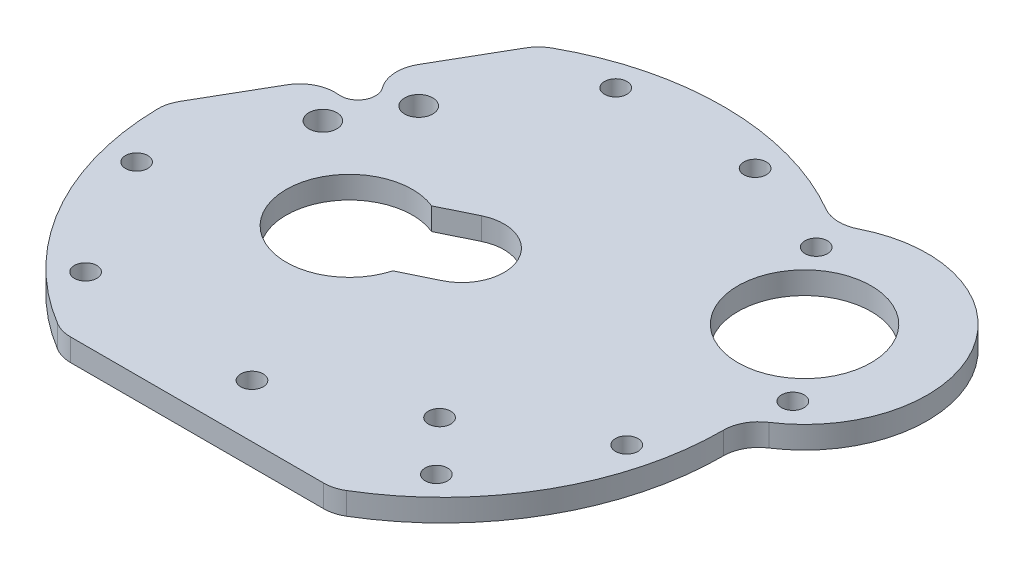
SolidWorks part; units mm, degrees
ref_plane "Front Plane" through (0, 0, 0) normal (0, 0, 1) x (1, 0, 0)
ref_plane "Top Plane" through (0, 0, 0) normal (0, 1, 0) x (1, 0, 0)
ref_plane "Right Plane" through (0, 0, 0) normal (1, 0, 0) x (0, 0, -1)
sketch "Sketch2" plane through (0, 0, 0) normal (0, 1, 0) x (1, 0, 0)
  line L0 (-20.6284, 34.2705) -> (-39.9933, 0.7295)
  line L1 (-19.3649, -35) -> (19.3649, -35)
  line L2 (0, 0) -> (-9.9332, 34.6025) construction
  line L3 (0, 0) -> (-34.9332, -8.6988) construction
  line L4 (0, 0) -> (32.7032, 18.8812) construction
  line L5 (0, 40) -> (0, 0) construction
  line L6 (0.2426, -27.4303) -> (18.2185, -18.6629) construction
  line L7 (0, 0) -> (10.8543, -22.2546) construction
  line L8 (-1.1037, 3.8447) -> (-11.8892, -1.4157) construction
  line L9 (24.0255, 29.2228) -> (41.3808, 8.5396) construction
  line L10 (32.7032, 18.8812) -> (32.7032, 36.3812) construction
  line L11 (-9.9332, 34.6025) -> (-34.9332, -8.6988) construction
  line L12 (0, 0) -> (-22.4332, 12.9518) construction
  line L13 (-25, -25.9037) -> (25, -25.9037) construction
  line L14 (0, 0) -> (0, -25.9037) construction
  line L15 (-3.7339, 9.2375) -> (-8.4902, 6.9177)
  line L16 (1.5265, -1.548) -> (-3.2297, -3.8678)
  arc A0 (-39.9933, 0.7295) -> (-19.3649, -35) centre (0, 0) ccw
  circle A1 centre (0.2426, -27.4303) radius 1.6 construction
  arc A2 (39.8928, 2.9263) -> (22.4806, 33.0851) centre (32.7032, 18.8812) ccw
  circle A3 centre (32.7032, 18.8812) radius 9.5
  circle A4 centre (-9.9332, 34.6025) radius 1.6
  circle A5 centre (34.9332, -8.6988) radius 1.6
  circle A6 centre (24.0255, 29.2228) radius 1.6
  circle A7 centre (41.3808, 8.5396) radius 1.6
  circle A8 centre (9.9332, 34.6025) radius 1.6
  circle A9 centre (18.2185, -18.6629) radius 1.6
  circle A10 centre (-25, -25.9037) radius 1.6
  circle A11 centre (0.2426, -27.4303) radius 1.6
  circle A12 centre (25, -25.9037) radius 1.6
  circle A13 centre (-34.9332, -8.6988) radius 1.6
  arc A15 (-8.4902, 6.9177) -> (-3.2297, -3.8678) centre (-11.8892, -1.4157) ccw
  arc A16 (1.5265, -1.548) -> (-3.7339, 9.2375) centre (-1.1037, 3.8447) ccw
  arc A17 (19.3649, -35) -> (39.8928, 2.9263) centre (0, 0) ccw
  circle A18 centre (0, 0) radius 36 construction
  arc A19 (22.4806, 33.0851) -> (-20.6284, 34.2705) centre (0, 0) ccw
  circle A20 centre (32.7032, 18.8812) radius 13.5 construction
  circle A21 centre (18.2185, -18.6629) radius 1.6 construction
  arc A23 (38.9209, 2.523) -> (46.7298, 29.3455) centre (32.7032, 18.8812) ccw construction
  point P9 (32.7032, 18.8812)
  point P18 (0, 36)
  point P34 (0, 0)
  dimension "D1" = 40
  dimension "D2" = 50
  dimension "D3" = 37
  dimension "D4" = 19
  dimension "D5" = 12
  dimension "D6" = 9
  dimension "D7" = 4
  dimension "D15" = 27
  dimension "D18" = 4
  dimension "D19" = 3.2
  dimension "D23" = 35
  dimension "D9" = 12
  dimension "D8" = 60
  dimension "D13" = 60
  dimension "D14" = 40
  dimension "D17" = 3
  dimension "D20" = 120
  dimension "D22" = 35
extrude "Boss-Extrude1" add sketch "Sketch2" along normal blind 3.175
fillet "Fillet1" radius 5 2 edges at (22.4806, 1.5875, -33.0851) (39.8928, 1.5875, -2.9263)
sketch "Sketch3" plane through (0, 3.175, 0) normal (0, 1, 0) x (1, 0, 0)
  line L0 (-30.3109, 17.5) -> (0, 0) construction
  line L1 (-20.6284, 34.2705) -> (-39.9933, 0.7295) construction
  line L2 (-21.7487, 18.3301) -> (-26.7487, 9.6699) construction
  line L3 (-30.3109, 17.5) -> (-28.5788, 16.5) construction
  line L4 (-29.0609, 19.6651) -> (-27.3288, 18.6651)
  line L5 (-31.5609, 15.3349) -> (-29.8288, 14.3349)
  circle A0 centre (-26.7487, 9.6699) radius 2
  circle A1 centre (-21.7487, 18.3301) radius 2
  arc A2 (-29.0609, 19.6651) -> (-31.5609, 15.3349) centre (-30.3109, 17.5) ccw
  arc A3 (-29.8288, 14.3349) -> (-27.3288, 18.6651) centre (-28.5788, 16.5) ccw
  point P9 (-24.2487, 14)
  point P10 (-29.4449, 17)
  dimension "D1" = 4
  dimension "D2" = 2.5
  dimension "D4" = 10
  dimension "D3" = 2
  dimension "D5" = 5
extrude "Cut-Extrude1" cut sketch "Sketch3" against normal up to next
fillet "Fillet2" radius 5 6 edges at (-31.5609, 1.5875, -15.3349) (-29.0609, 1.5875, -19.6651) (19.3649, 1.5875, 35) (-19.3649, 1.5875, 35) (-39.9933, 1.5875, -0.7295) (-20.6284, 1.5875, -34.2705)
